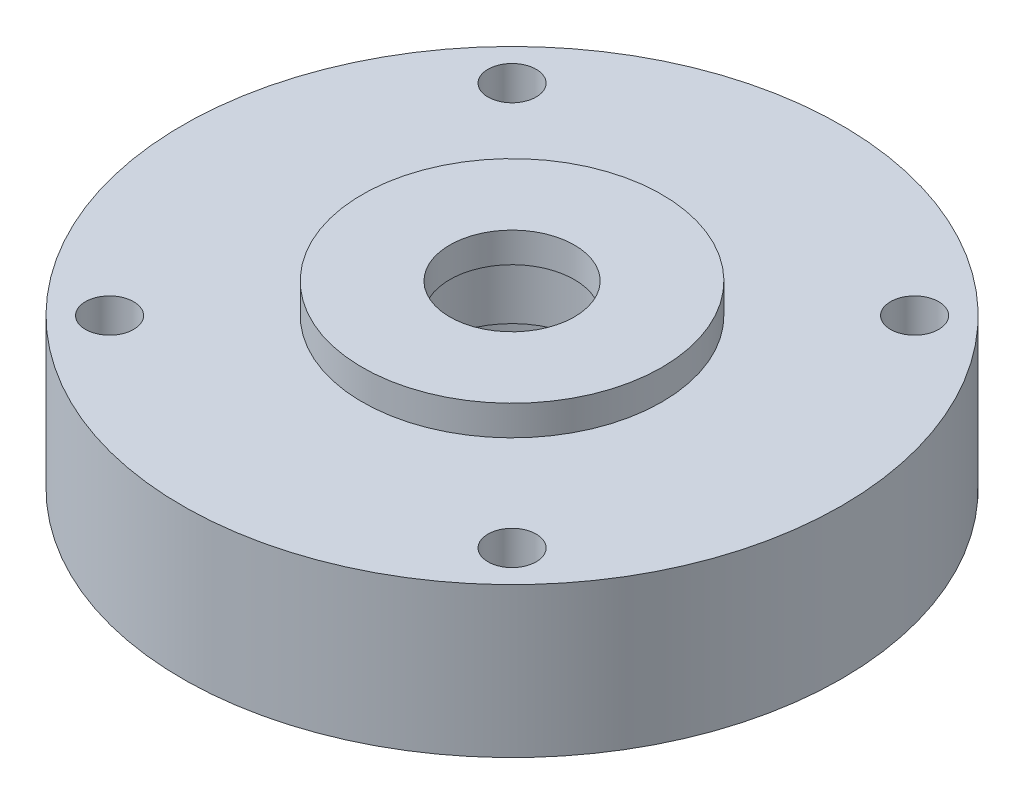
SolidWorks part; units mm, degrees
other "Markup1"
sketch "Sketch2" plane through (28.575, 0, 28.575) normal (0.2444, -0.6972, 0.6739) x (0.9588, 0.0701, -0.2753)
material "6061-T6 (SS)"
ref_plane "Front Plane" through (0, 0, 0) normal (0, 0, 1) x (1, 0, 0)
ref_plane "Top Plane" through (0, 0, 0) normal (0, 1, 0) x (1, 0, 0)
ref_plane "Right Plane" through (0, 0, 0) normal (1, 0, 0) x (0, 0, -1)
sketch "Sketch1" plane through (0, 0, 0) normal (0, 0, 1) x (1, 0, 0)
  line L0 (0, 0) -> (0, 19.05) construction
  line L3 (-15.875, 19.05) -> (-6.604, 19.05)
  line L4 (-6.604, 19.05) -> (-6.604, 15.875)
  line L5 (-6.604, 15.875) -> (-7.9375, 15.875)
  line L6 (-7.9375, 15.875) -> (-7.9375, 9.525)
  line L7 (-15.875, 19.05) -> (-15.875, 15.875)
  line L8 (-15.875, 15.875) -> (-34.925, 15.875)
  line L9 (-34.925, 15.875) -> (-34.925, 0)
  line L10 (-7.9375, 9.525) -> (-15.0125, 9.525)
  line L15 (-20.6375, 0) -> (-15.0125, 0)
  line L16 (-15.0125, 0) -> (-15.0125, 9.525)
  line L17 (-34.925, 0) -> (-25.4, 0)
  line L18 (-25.4, 0) -> (-25.4, 3.1369)
  line L19 (-25.4, 3.1369) -> (-20.6375, 3.1369)
  line L20 (-20.6375, 3.1369) -> (-20.6375, 0)
  dimension "D1" = 13.208
  dimension "D2" = 30.025
  dimension "D3" = 15.875
  dimension "D4" = 3.175
  dimension "D5" = 3.175
  dimension "D6" = 19.05
  dimension "D7" = 69.85
  dimension "D8" = 6.35
  dimension "D9" = 4.7625
  dimension "D10" = 9.525
  dimension "D12" = 50.8
  dimension "D13" = 3.1369
revolve "Revolve1" add sketch "Sketch1" angle 360 about L0
hole_wizard "#10 Clearance Hole1" positions "Sketch3" profile "Sketch4" hole size "#10" standard "ANSI Inch" end condition through all
sketch "Sketch3" plane through (0, 15.875, 0) normal (0, 1, 0) x (1, 0, 0)
  line L0 (-21.3281, 21.3281) -> (21.3281, -21.3281) construction
  line L1 (-21.3281, -21.3281) -> (21.3281, 21.3281) construction
  line L2 (0, 0) -> (-34.925, 0) construction
  circle A0 centre (0, 0) radius 34.925 construction
  point P0 (-21.3281, 21.3281)
  point P2 (21.3281, 21.3281)
  point P4 (21.3281, -21.3281)
  point P6 (-21.3281, -21.3281)
  point P14 (0, 0)
  point P16 (0, 0)
  dimension "D1" = 45
  dimension "D2" = 60.325
sketch "Sketch4" plane through (-21.3281, 15.875, -21.3281) normal (1, 0, 0) x (0, 0, 1)
  line L0 (0, 0) -> (0, 15.875)
  line L1 (0, 15.875) -> (2.5527, 15.875)
  line L2 (2.5527, 15.875) -> (2.5527, 0)
  line L5 (2.5527, 0) -> (0, 0)
  line L11 (0, -6.35) -> (0, 107.95) construction
  dimension "Thru Hole Dia." = 5.1054
  dimension "Thru Hole Depth" = 15.875
sketch "Sketch5" plane through (0, 0, 0) normal (0, 1, 0) x (1, 0, 0)
  circle A0 centre (0, 0) radius 38.1
  dimension "D1" = 76.2
ref_plane "Plane1" through (0, 0, 0) normal (0, -1, 0) x (-1, 0, 0)
